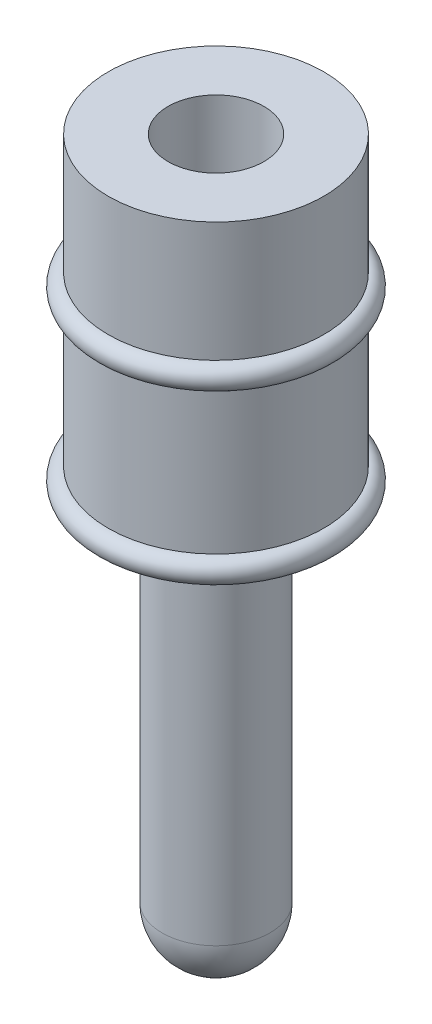
SolidWorks part; units mm, degrees
ref_plane "Ebene vorne" through (0, 0, 0) normal (0, 0, 1) x (1, 0, 0)
ref_plane "Ebene oben" through (0, 0, 0) normal (0, 1, 0) x (1, 0, 0)
ref_plane "Ebene rechts" through (0, 0, 0) normal (1, 0, 0) x (0, 0, -1)
sketch "Skizze1" plane through (0, 0, 0) normal (0, 0, 1) x (1, 0, 0)
  line L0 (-2.25, 15) -> (-2.25, 8.5)
  line L1 (-2.25, 8.5) -> (-1.125, 8)
  line L2 (-1.125, 8) -> (-1.125, 1.125)
  line L3 (0, 0) -> (0, 15)
  line L4 (0, 15) -> (-2.25, 15)
  arc A0 (-1.125, 1.125) -> (0, 0) centre (0, 1.125) ccw
  dimension "D1" = 7
  dimension "D2" = 8
  dimension "D3" = 2.25
  dimension "D4" = 1.125
  dimension "D5" = 0.5
revolve "Rotation1" add sketch "Skizze1" angle 360 about L3
sketch "Skizze2" plane through (0, 0, 0) normal (0, 0, 1) x (1, 0, 0)
  line L0 (0, 15) -> (0, 11)
  line L1 (2.25, 15) -> (-2.25, 15) construction
  line L2 (0, 11) -> (-1.375, 11)
  line L3 (-1.375, 11) -> (-1.375, 13)
  line L4 (-1.375, 13) -> (-1, 13)
  line L5 (-1, 13) -> (-1, 15)
  line L6 (-1, 15) -> (0, 15)
  dimension "D1" = 2
  dimension "D2" = 4
  dimension "D3" = 1.375
  dimension "D4" = 1
revolve "Schnitt-Rotation1" cut sketch "Skizze2" angle 360 about L0
sketch "Skizze3" plane through (0, 0, 0) normal (0, 0, 1) x (1, 0, 0)
  line L0 (0, 0) -> (0, 6.0007) construction
  line L1 (-2.25, 15) -> (-2.25, 8.5) construction
  line L2 (-2.25, 12.5) -> (-2.25, 12)
  line L3 (-2.25, 15) -> (-2.25, 8.5) construction
  line L5 (-2.25, 9) -> (-2.25, 8.5)
  arc A2 (-2.25, 12.5) -> (-2.25, 12) centre (-2.25, 12.25) ccw
  arc A3 (-2.25, 9) -> (-2.25, 8.5) centre (-2.25, 8.75) ccw
  dimension "D1" = 0.25
  dimension "D2" = 3
revolve "Rotation2" add sketch "Skizze3" angle 360 about L0
